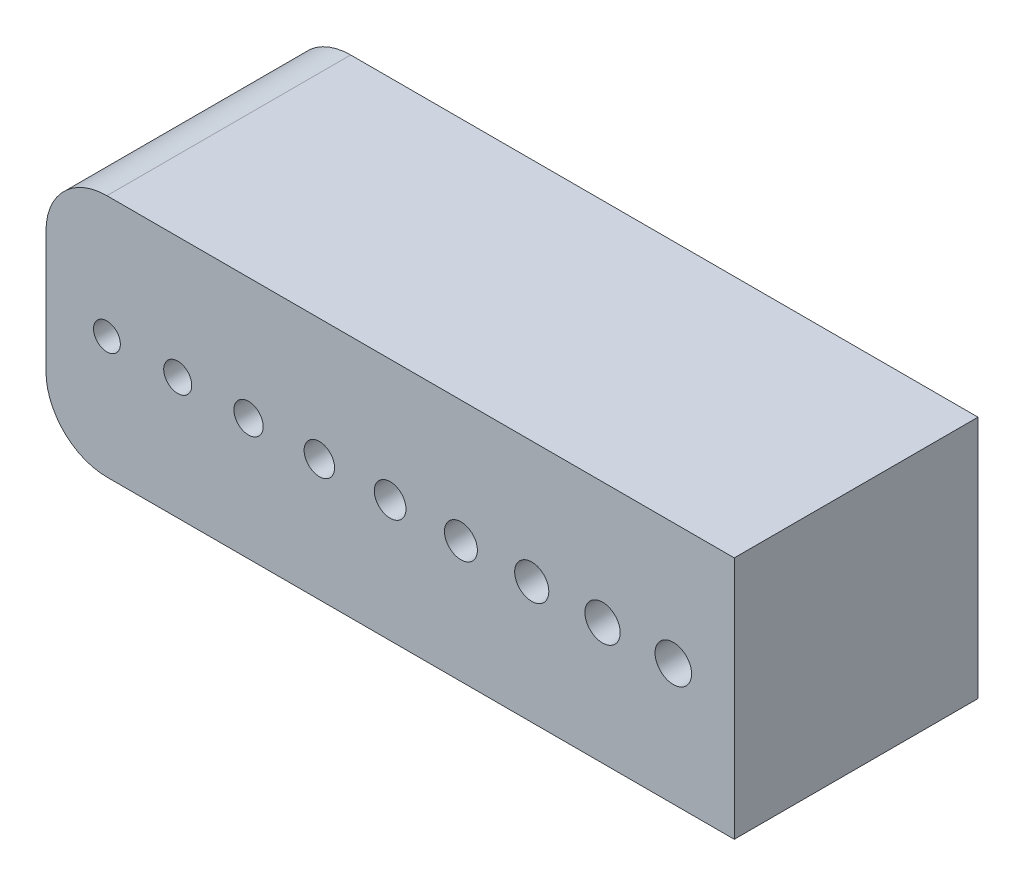
SolidWorks part; units mm, degrees
ref_plane "Front Plane" through (0, 0, 0) normal (0, 0, 1) x (1, 0, 0)
ref_plane "Top Plane" through (0, 0, 0) normal (0, 1, 0) x (1, 0, 0)
ref_plane "Right Plane" through (0, 0, 0) normal (1, 0, 0) x (0, 0, -1)
sketch "Sketch1" plane through (0, 0, 0) normal (0, 0, 1) x (1, 0, 0)
  line L0 (-1000, 0) -> (49000, 0) construction
  line L1 (-23.2382, -10) -> (28.2382, -10)
  line L2 (-28.2382, -5) -> (-28.2382, 5)
  line L3 (-23.2382, 10) -> (28.2382, 10)
  line L4 (28.2382, -10) -> (28.2382, 10)
  line L5 (-28.2382, -10) -> (28.2382, 10) construction
  line L6 (-28.2382, 10) -> (28.2382, -10) construction
  line L7 (-23.2382, 10) -> (-23.2382, -10) construction
  line L8 (-17.4287, 10) -> (-17.4287, -10) construction
  line L9 (-11.6191, 10) -> (-11.6191, -10) construction
  line L10 (-5.8096, 10) -> (-5.8096, -10) construction
  line L11 (0, 10) -> (0, -10) construction
  line L12 (5.8096, 10) -> (5.8096, -10) construction
  line L13 (11.6191, 10) -> (11.6191, -10) construction
  line L14 (17.4287, 10) -> (17.4287, -10) construction
  line L15 (23.2382, 10) -> (23.2382, -10) construction
  circle A0 centre (-23.2382, 0) radius 1.1
  circle A1 centre (-17.4287, 0) radius 1.15
  circle A2 centre (-11.6191, 0) radius 1.2
  circle A3 centre (-5.8096, 0) radius 1.25
  circle A4 centre (0, 0) radius 1.3
  circle A5 centre (5.8096, 0) radius 1.35
  circle A6 centre (11.6191, 0) radius 1.4
  circle A7 centre (17.4287, 0) radius 1.45
  circle A8 centre (23.2382, 0) radius 1.5
  arc A9 (-23.2382, -10) -> (-28.2382, -5) centre (-23.2382, -5) cw
  arc A10 (-28.2382, 5) -> (-23.2382, 10) centre (-23.2382, 5) cw
  point P0 (0, 0)
  dimension "D5" = 3
  dimension "D6" = 2.9
  dimension "D7" = 2.8
  dimension "D8" = 2.7
  dimension "D9" = 2.6
  dimension "D10" = 2.5
  dimension "D11" = 2.4
  dimension "D12" = 2.3
  dimension "D13" = 2.2
  dimension "D14" = 5
  dimension "D1" = 20
  dimension "D2" = 5
  dimension "D3" = 9
  dimension "D4" = 5
extrude "Boss-Extrude1" add sketch "Sketch1" along normal blind 20
